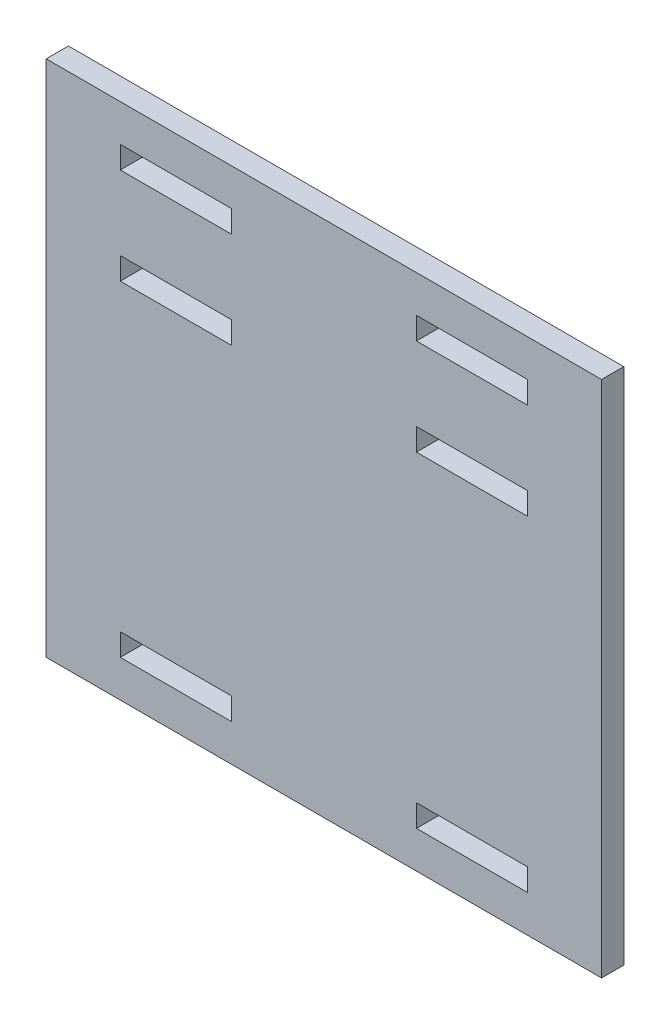
SolidWorks part; units mm, degrees
ref_plane "Front Plane" through (0, 0, 0) normal (0, 0, 1) x (1, 0, 0)
ref_plane "Top Plane" through (0, 0, 0) normal (0, 1, 0) x (1, 0, 0)
ref_plane "Right Plane" through (0, 0, 0) normal (1, 0, 0) x (0, 0, -1)
sketch "Esquisse1" plane through (0, 0, 0) normal (0, 0, 1) x (1, 0, 0)
  line L1 (-50.1837, 32.1633) -> (24.8163, 32.1633)
  line L2 (-50.1837, 32.1633) -> (-50.1837, -37.8367)
  line L3 (-50.1837, -37.8367) -> (24.8163, -37.8367)
  line L4 (24.8163, 32.1633) -> (24.8163, -37.8367)
  line L5 (-40.1837, 27.1633) -> (-25.1837, 27.1633)
  line L6 (-40.1837, 27.1633) -> (-40.1837, 24.1633)
  line L7 (-40.1837, 24.1633) -> (-25.1837, 24.1633)
  line L8 (-25.1837, 27.1633) -> (-25.1837, 24.1633)
  line L9 (-0.1837, 27.1633) -> (14.8163, 27.1633)
  line L10 (-0.1837, 27.1633) -> (-0.1837, 24.1633)
  line L11 (-0.1837, 24.1633) -> (14.8163, 24.1633)
  line L12 (14.8163, 27.1633) -> (14.8163, 24.1633)
  line L13 (-0.1837, -29.8367) -> (14.8163, -29.8367)
  line L14 (-0.1837, -29.8367) -> (-0.1837, -32.8367)
  line L15 (-0.1837, -32.8367) -> (14.8163, -32.8367)
  line L16 (14.8163, -29.8367) -> (14.8163, -32.8367)
  line L17 (-25.1837, -29.8367) -> (-40.1837, -29.8367)
  line L18 (-25.1837, -29.8367) -> (-25.1837, -32.8367)
  line L19 (-25.1837, -32.8367) -> (-40.1837, -32.8367)
  line L20 (-40.1837, -29.8367) -> (-40.1837, -32.8367)
  line L21 (-40.1837, 14.1633) -> (-25.1837, 14.1633)
  line L22 (-40.1837, 14.1633) -> (-40.1837, 11.1633)
  line L23 (-40.1837, 11.1633) -> (-25.1837, 11.1633)
  line L24 (-25.1837, 14.1633) -> (-25.1837, 11.1633)
  line L25 (-0.1837, 11.1633) -> (14.8163, 11.1633)
  line L26 (-0.1837, 11.1633) -> (-0.1837, 14.1633)
  line L27 (-0.1837, 14.1633) -> (14.8163, 14.1633)
  line L28 (14.8163, 11.1633) -> (14.8163, 14.1633)
  dimension "D1" = 75
  dimension "D2" = 70
  dimension "D3" = 3
  dimension "D4" = 3
  dimension "D5" = 5
  dimension "D6" = 5
  dimension "D7" = 10
  dimension "D8" = 25
  dimension "D9" = 10
  dimension "D10" = 15
  dimension "D11" = 3
  dimension "D12" = 5
  dimension "D13" = 5
  dimension "D14" = 15
  dimension "D15" = 15
  dimension "D16" = 25
  dimension "D17" = 10
  dimension "D18" = 3
  dimension "D19" = 10
  dimension "D20" = 10
  dimension "D21" = 3
  dimension "D22" = 3
extrude "Boss.-Extru.1" add sketch "Esquisse1" along normal blind 3
